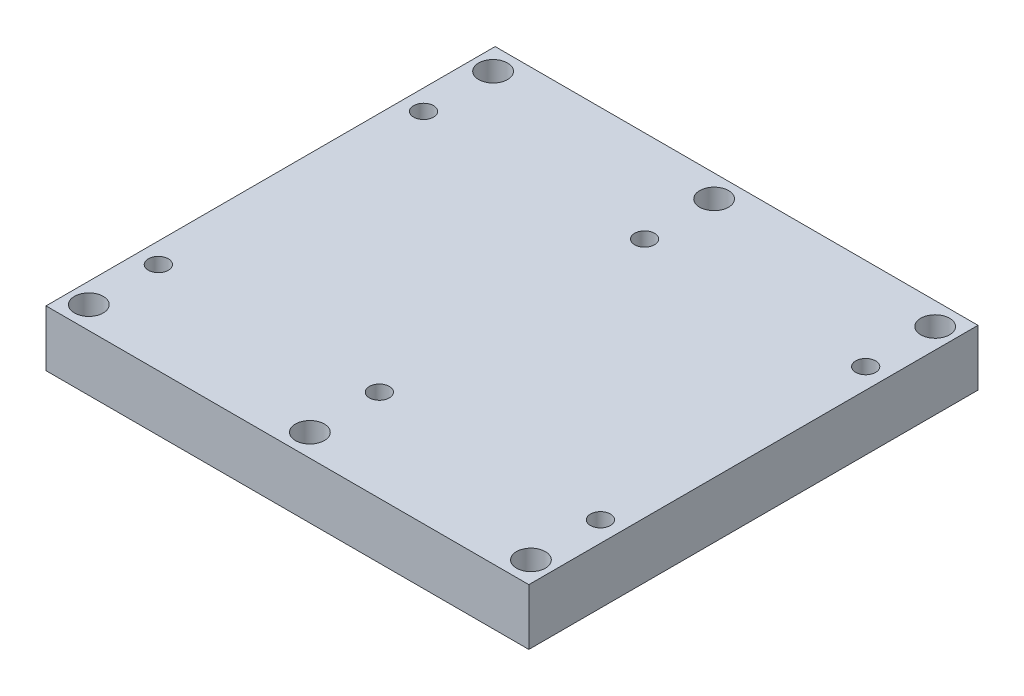
SolidWorks part; units mm, degrees
material "C110 COPPER"
ref_plane "Front Plane" through (0, 0, 0) normal (0, 0, 1) x (1, 0, 0)
ref_plane "Top Plane" through (0, 0, 0) normal (0, 1, 0) x (1, 0, 0)
ref_plane "Right Plane" through (0, 0, 0) normal (1, 0, 0) x (0, 0, -1)
sketch "Sketch1" plane through (0, 0, 0) normal (0, 1, 0) x (1, 0, 0)
  line L1 (-27.305, -25.4) -> (27.305, -25.4)
  line L2 (-27.305, -25.4) -> (-27.305, 25.4)
  line L3 (-27.305, 25.4) -> (27.305, 25.4)
  line L4 (27.305, -25.4) -> (27.305, 25.4)
  line L5 (-27.305, -25.4) -> (27.305, 25.4) construction
  line L6 (-27.305, 25.4) -> (27.305, -25.4) construction
  point P0 (0, 0)
  dimension "D1" = 50.8
  dimension "D2" = 54.61
extrude "Boss-Extrude1" add sketch "Sketch1" along normal blind 6.35
hole_wizard "#4-40 Tapped Hole1" positions "Sketch2" profile "Sketch3" tap size "#4-40" standard "ANSI Inch" end condition up to next
sketch "Sketch2" plane through (0, 6.35, 0) normal (0, 1, 0) x (1, 0, 0)
  point P0 (-25, 15)
  point P30 (0, 15)
  point P31 (25, 15)
  point P32 (0, -15)
  point P33 (25, -15)
  point P36 (-25, -15)
  point P45 (0, 0)
  point P46 (0, 0)
  point P47 (0, 0)
  point P48 (0, 0)
  point P49 (0, 0)
  dimension "D1" = 25
  dimension "D2" = 15
  dimension "D5" = 25
  dimension "D6" = 30
  dimension "D3" = 3
  dimension "D4" = 2
sketch "Sketch3" plane through (-25, 6.35, -15) normal (1, 0, 0) x (0, 0, 1)
  line L0 (0, 0) -> (0, 6.35)
  line L1 (0, 6.35) -> (1.1303, 6.35)
  line L2 (1.1303, 6.35) -> (1.1303, 0)
  line L5 (1.1303, 0) -> (0, 0)
  line L11 (0, -6.35) -> (0, 107.95) construction
  dimension "Thru Tap Drill Dia." = 2.2606
  dimension "Thru Tap Drill Depth" = 6.35
cosmetic thread "Hole Thread1" parameters "D2"=2.8448
cosmetic thread "Hole Thread2" parameters "D2"=2.8448
cosmetic thread "Hole Thread5" parameters "D2"=2.8448
cosmetic thread "Hole Thread6" parameters "D2"=2.8448
cosmetic thread "Hole Thread7" parameters "D2"=2.8448
cosmetic thread "Hole Thread8" parameters "D2"=2.8448
hole_wizard "#4 Clearance Hole1" positions "Sketch4" profile "Sketch5" hole size "#4" standard "ANSI Inch" end condition up to next
sketch "Sketch4" plane through (0, 6.35, 0) normal (0, 1, 0) x (1, 0, 0)
  point P0 (-25, 22.86)
  point P12 (0, 22.86)
  point P13 (25, 22.86)
  point P14 (0, -22.86)
  point P15 (25, -22.86)
  point P16 (-25, -22.86)
  point P17 (0, 0)
  point P18 (0, 0)
  dimension "D1" = 25
  dimension "D2" = 22.86
  dimension "D5" = 25
  dimension "D6" = 45.72
  dimension "D3" = 3
  dimension "D4" = 2
sketch "Sketch5" plane through (-25, 6.35, -22.86) normal (1, 0, 0) x (0, 0, 1)
  line L0 (0, 0) -> (0, 6.35)
  line L1 (0, 6.35) -> (1.6319, 6.35)
  line L2 (1.6319, 6.35) -> (1.6319, 0)
  line L5 (1.6319, 0) -> (0, 0)
  line L11 (0, -6.35) -> (0, 107.95) construction
  dimension "Thru Hole Dia." = 3.2639
  dimension "Thru Hole Depth" = 6.35
